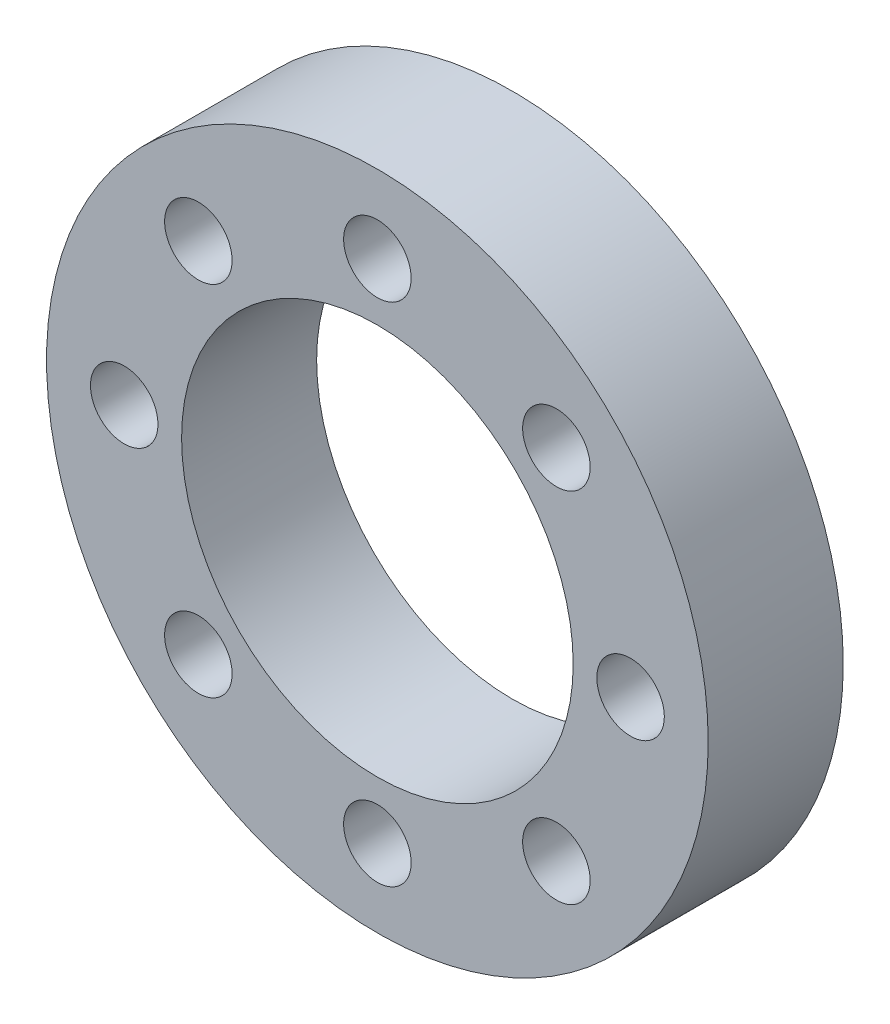
SolidWorks part; units mm, degrees
material "Copper"
ref_plane "Front Plane" through (0, 0, 0) normal (0, 0, 1) x (1, 0, 0)
ref_plane "Top Plane" through (0, 0, 0) normal (0, 1, 0) x (1, 0, 0)
ref_plane "Right Plane" through (0, 0, 0) normal (1, 0, 0) x (0, 0, -1)
sketch "Sketch1" plane through (0, 0, 0) normal (0, 0, 1) x (1, 0, 0)
  circle A0 centre (0, 0) radius 9.8
  circle A1 centre (0, 0) radius 5.8
  dimension "D1" = 11.6
  dimension "D2" = 19.6
extrude "Boss-Extrude1" add sketch "Sketch1" along normal blind 4 contours A1
sketch "Sketch2" plane through (0, 0, 4) normal (0, 0, 1) x (1, 0, 0)
  line L0 (0, 0) -> (-5.3033, 5.3033) construction
  line L1 (-7.5, 0) -> (7.5, 0) construction
  circle A0 centre (0, 7.5) radius 1
  circle A1 centre (0, 0) radius 7.5 construction
  circle A2 centre (7.5, 0) radius 1
  circle A3 centre (0, -7.5) radius 1
  circle A4 centre (-7.5, 0) radius 1
  circle A5 centre (-5.3033, 5.3033) radius 1
  circle A6 centre (5.3033, 5.3033) radius 1
  circle A7 centre (5.3033, -5.3033) radius 1
  circle A8 centre (-5.3033, -5.3033) radius 1
  point P14 (0, 0)
  point P23 (0, 0)
  dimension "D1" = 2
  dimension "D2" = 7.5
  dimension "D3" = 15
  dimension "D5" = 2
  dimension "D6" = 45
  dimension "D4" = 4
  dimension "D7" = 4
extrude "Cut-Extrude1" cut sketch "Sketch2" against normal through all
